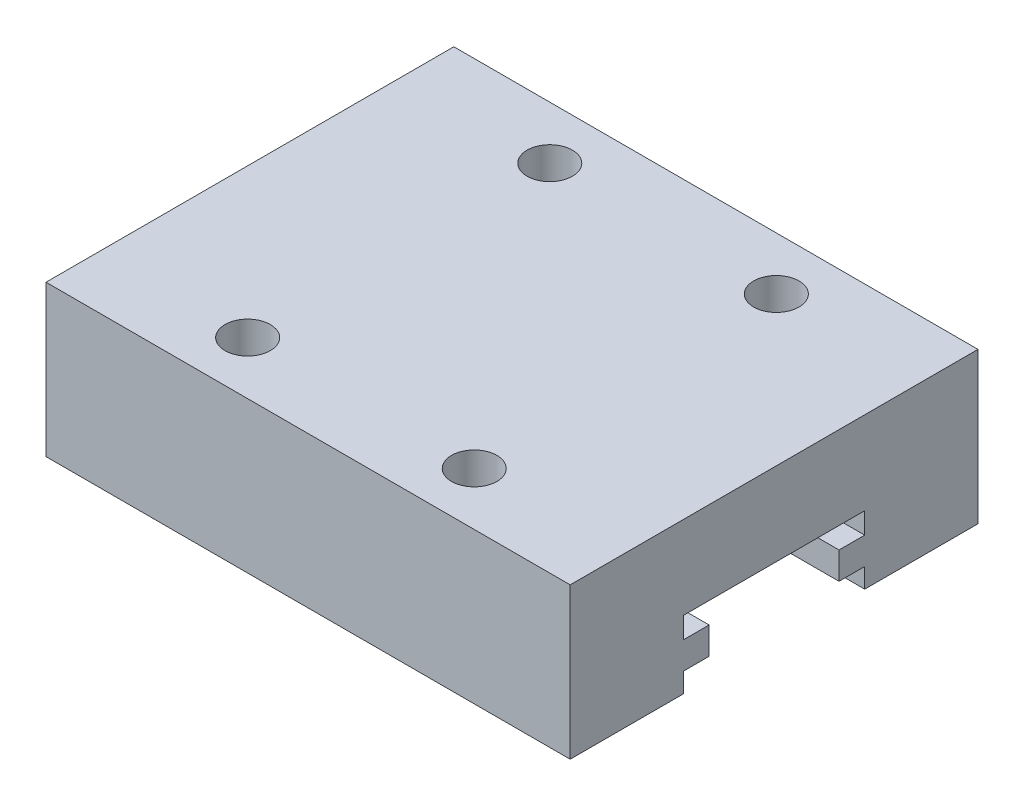
SolidWorks part; units mm, degrees
ref_plane "Alzado" through (0, 0, 0) normal (0, 0, 1) x (1, 0, 0)
ref_plane "Planta" through (0, 0, 0) normal (0, 1, 0) x (1, 0, 0)
ref_plane "Vista lateral" through (0, 0, 0) normal (1, 0, 0) x (0, 0, -1)
sketch "Croquis1" plane through (0, 0, 0) normal (0, 1, 0) x (1, 0, 0)
  line L2 (0, 0) -> (34.7, 0)
  line L3 (0, 0) -> (0, 27)
  line L4 (0, 27) -> (34.7, 27)
  line L5 (34.7, 0) -> (34.7, 27)
  dimension "D1" = 34.7
  dimension "D2" = 27
extrude "Saliente-Extruir1" add sketch "Croquis1" along normal blind 10
sketch "Croquis2" plane through (0, 10, 0) normal (0, 1, 0) x (1, 0, 0)
  line L0 (0, 0) -> (34.7, 0) construction
  line L1 (34.7, 0) -> (34.7, 27) construction
  line L2 (34.7, 27) -> (0, 27) construction
  line L3 (0, 27) -> (0, 0) construction
  circle A0 centre (9.85, 23.5) radius 1.5
  circle A1 centre (24.85, 23.5) radius 1.5
  circle A2 centre (9.85, 3.5) radius 1.5
  circle A3 centre (24.85, 3.5) radius 1.5
  dimension "D1" = 3
  dimension "D2" = 9.85
  dimension "D3" = 3.5
  dimension "D4" = 3.5
  dimension "D5" = 9.85
  dimension "D6" = 3.5
  dimension "D7" = 3.5
  dimension "D8" = 9.85
  dimension "D10" = 9.85
extrude "Cortar-Extruir1" cut sketch "Croquis2" against normal blind 5
sketch "Croquis3" plane through (34.7, 0, 0) normal (1, 0, 0) x (0, 0, -1)
  line L0 (0, 0) -> (27, 0) construction
  line L1 (7.5, 0) -> (19.5, 0)
  line L2 (7.5, 0) -> (7.5, 1.3)
  line L3 (7.5, 4.5) -> (19.5, 4.5)
  line L4 (19.5, 0) -> (19.5, 1.3)
  line L5 (13.5, 10) -> (13.5, 0) construction
  line L6 (0, 10) -> (27, 10) construction
  line L7 (7.5, 3.1) -> (7.5, 4.5)
  line L8 (7.5, 3.1) -> (9.2, 3.1)
  line L10 (7.5, 1.3) -> (9.2, 1.3)
  line L11 (9.2, 3.1) -> (9.2, 1.3)
  line L12 (19.5, 1.3) -> (17.8, 1.3)
  line L13 (19.5, 3.1) -> (17.8, 3.1)
  line L14 (17.8, 3.1) -> (17.8, 1.3)
  line L15 (19.5, 3.1) -> (19.5, 4.5)
  dimension "D2" = 4.5
  dimension "D3" = 6
  dimension "D4" = 1.8
  dimension "D5" = 1.7
  dimension "D6" = 1.4
extrude "Cortar-Extruir2" cut sketch "Croquis3" against normal up to surface (34.7 mm away) up to face at (0, 5, -13.5)
